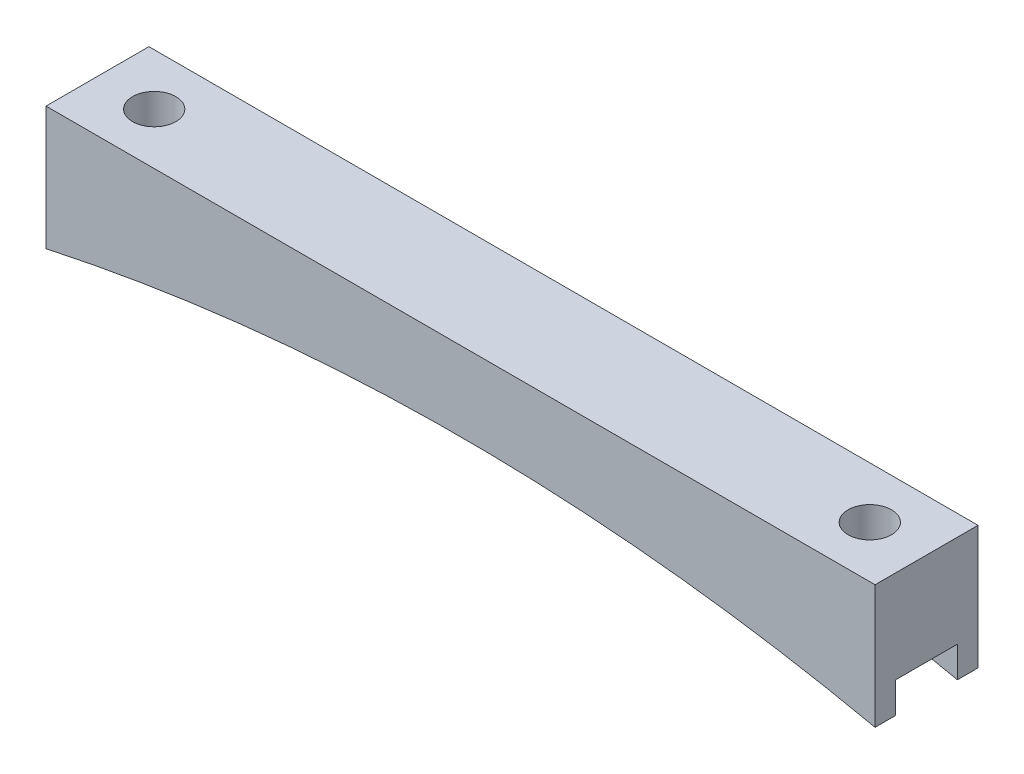
SolidWorks part; units mm, degrees
ref_plane "Front Plane" through (0, 0, 0) normal (0, 0, 1) x (1, 0, 0)
ref_plane "Top Plane" through (0, 0, 0) normal (0, 1, 0) x (1, 0, 0)
ref_plane "Right Plane" through (0, 0, 0) normal (1, 0, 0) x (0, 0, -1)
sketch "Sketch1" plane through (0, 0, 0) normal (0, 0, 1) x (1, 0, 0)
  line L0 (-51.145, 0) -> (51.145, 0)
  line L1 (-44.145, -2.54) -> (44.145, -2.54) construction
  line L2 (0, 0) -> (0, -4.6068) construction
  line L3 (51.145, 0) -> (51.145, -15.24)
  line L4 (-51.145, 0) -> (-51.145, -15.24)
  arc A0 (-51.145, -15.24) -> (51.145, -15.24) centre (0, -251.0575) cw
  point P4 (0, 0)
  point P9 (0, -2.54)
  dimension "D4" = 241.3
  dimension "D1" = 88.29
  dimension "D2" = 2.54
  dimension "D3" = 7
  dimension "D5" = 15.24
extrude "Boss-Extrude1" add sketch "Sketch1" along normal blind 12.7
sketch "Sketch2" plane through (0, 0, 0) normal (0, 1, 0) x (1, 0, 0)
  line L1 (-44.145, 0) -> (-44.145, -12.7) construction
  line L2 (-51.145, 0) -> (51.145, 0) construction
  line L3 (51.145, -12.7) -> (-51.145, -12.7) construction
  line L4 (44.145, 0) -> (44.145, -12.7) construction
  circle A0 centre (-44.145, -6.35) radius 2.675
  circle A1 centre (44.145, -6.35) radius 2.675
  circle A2 centre (-44.145, -6.35) radius 3 construction
  point P7 (-44.145, -6.35)
  dimension "D1" = 5.35
  dimension "D2" = 6
extrude "Cut-Extrude1" cut sketch "Sketch2" against normal through all
sketch "Sketch3" plane through (51.145, 0, 0) normal (1, 0, 0) x (0, 0, -1)
  line L0 (-12.7, -15.24) -> (0, -15.24) construction
  line L1 (-10.16, -15.24) -> (-2.54, -15.24)
  line L2 (-10.16, -15.24) -> (-10.16, -11.43)
  line L3 (-10.16, -11.43) -> (-2.54, -11.43)
  line L4 (-2.54, -15.24) -> (-2.54, -11.43)
  line L5 (-12.7, -15.24) -> (-12.7, 0) construction
  line L6 (0, -15.24) -> (0, 0) construction
  dimension "D1" = 2.54
  dimension "D2" = 2.54
  dimension "D3" = 3.81
extrude "Cut-Extrude2" cut sketch "Sketch3" against normal through all
